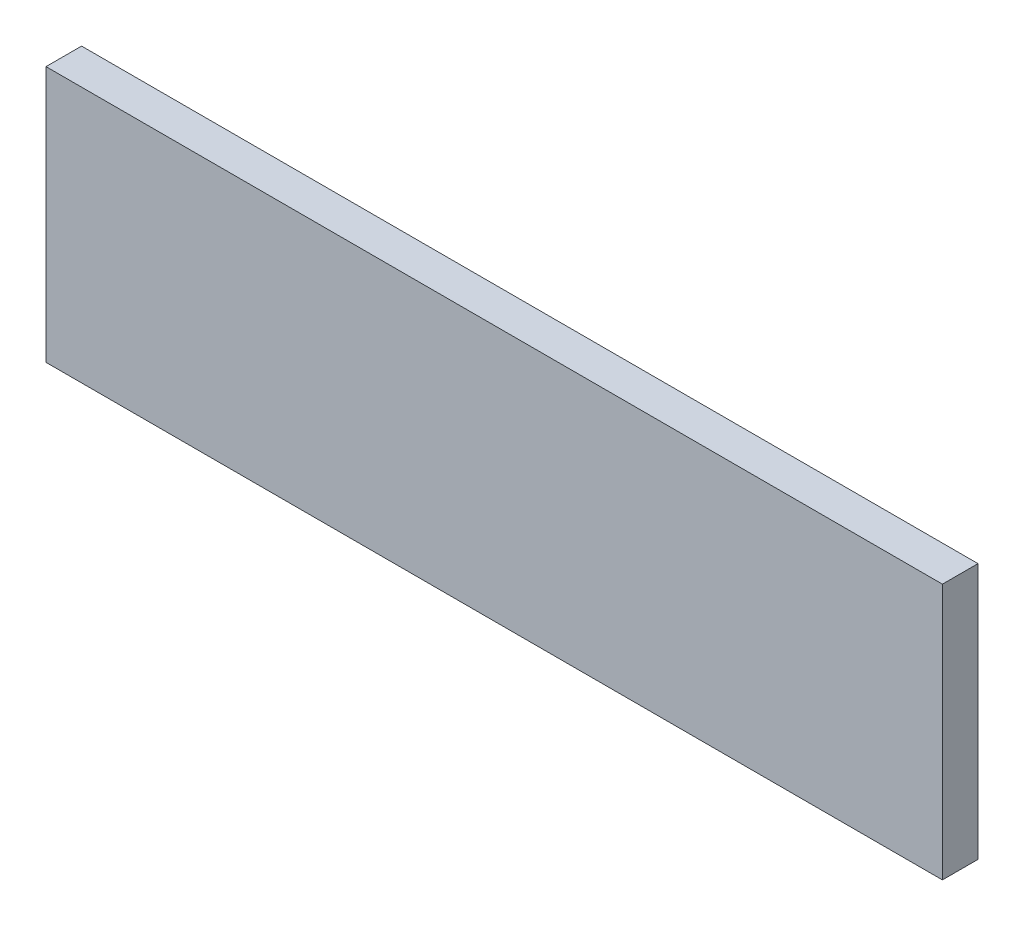
SolidWorks part; units mm, degrees
ref_plane "Front Plane" through (0, 0, 0) normal (0, 0, 1) x (1, 0, 0)
ref_plane "Top Plane" through (0, 0, 0) normal (0, 1, 0) x (1, 0, 0)
ref_plane "Right Plane" through (0, 0, 0) normal (1, 0, 0) x (0, 0, -1)
sketch "Sketch1" plane through (0, 0, 0) normal (0, 0, 1) x (1, 0, 0)
  line L1 (-64.8627, 12.0429) -> (-24.8627, 12.0429)
  line L2 (-64.8627, 12.0429) -> (-64.8627, 0.6129)
  line L3 (-64.8627, 0.6129) -> (-24.8627, 0.6129)
  line L4 (-24.8627, 12.0429) -> (-24.8627, 0.6129)
  dimension "D1" = 40
  dimension "D2" = 11.43
extrude "Boss-Extrude1" add sketch "Sketch1" along normal blind 1.5875
